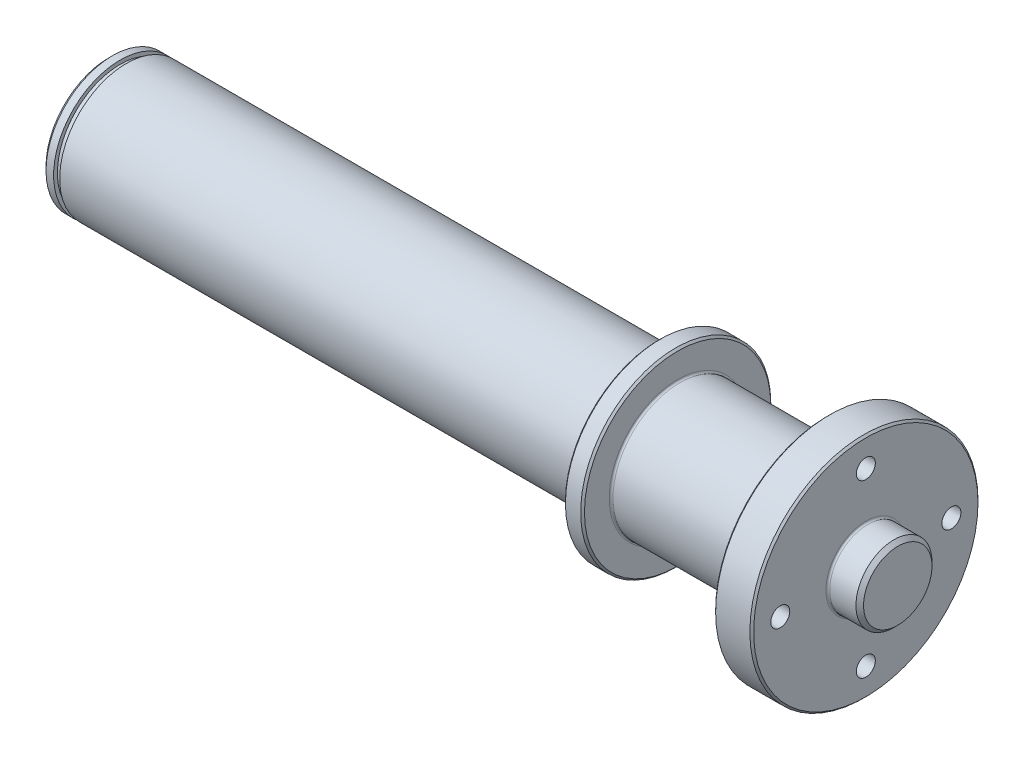
SolidWorks part; units mm, degrees
material "1.0037 (S235JR)"
ref_plane "Płaszczyzna przednia" through (0, 0, 0) normal (0, 0, 1) x (1, 0, 0)
ref_plane "Płaszczyzna górna" through (0, 0, 0) normal (0, 1, 0) x (1, 0, 0)
ref_plane "Płaszczyzna prawa" through (0, 0, 0) normal (1, 0, 0) x (0, 0, -1)
sketch "Szkic1" plane through (0, 0, 0) normal (0, 0, 1) x (1, 0, 0)
  line L0 (0, 0) -> (207.5, 0)
  line L1 (0, 0) -> (0, 17.5)
  line L2 (0, 17.5) -> (3, 17.5)
  line L3 (3, 17.5) -> (3, 16.5)
  line L4 (3, 16.5) -> (4.6, 16.5)
  line L5 (4.6, 16.5) -> (4.6, 17.5)
  line L6 (4.6, 17.5) -> (144.6, 17.5)
  line L7 (144.6, 17.5) -> (144.6, 25)
  line L8 (144.6, 25) -> (149.6, 25)
  line L9 (149.6, 25) -> (149.6, 17.5)
  line L10 (149.6, 17.5) -> (189.1, 17.5)
  line L11 (189.1, 17.5) -> (189.1, 30)
  line L12 (189.1, 30) -> (199.1, 30)
  line L13 (199.1, 30) -> (199.1, 10)
  line L14 (199.1, 10) -> (207.5, 10)
  line L15 (207.5, 10) -> (207.5, 0)
  line L16 (0, 0) -> (-14.1006, 0) construction
  dimension "D1" = 207.5
  dimension "D2" = 35
  dimension "D3" = 33
  dimension "D5" = 50
  dimension "D6" = 35
  dimension "D7" = 60
  dimension "D8" = 20
  dimension "D9" = 3
  dimension "D10" = 1.6
  dimension "D11" = 140
  dimension "D12" = 5
  dimension "D13" = 54.5
  dimension "D14" = 10
revolve "Obrót1" add sketch "Szkic1" angle 360 about L16
hole_wizard "Otwór gwintowany M63" positions "Szkic4" profile "Szkic6" tap size "M6" standard "DIN" end condition up to next
sketch "Szkic4" plane through (199.1, 0, 0) normal (1, 0, 0) x (0, 0, -1)
  line L0 (0, 0) -> (0, 22.5) construction
  circle A0 centre (0, 0) radius 22.5
  point P0 (0, 22.5)
  point P2 (22.5, 0)
  point P4 (0, -22.5)
  point P6 (-22.5, 0)
  dimension "D1" = 45
sketch "Szkic6" plane through (199.1, 22.5, 0) normal (0, 1, 0) x (0, 0, -1)
  line L0 (0, 0) -> (0, 10)
  line L1 (0, 10) -> (2.5, 10)
  line L2 (2.5, 10) -> (2.5, 0)
  line L5 (2.5, 0) -> (0, 0)
  line L11 (0, -6.35) -> (0, 107.95) construction
  dimension "Średnica otworu gwintowanego na wylot" = 5
  dimension "Głębokość otworu gwintowanego na wylot" = 10
cosmetic thread "Gwint otworu1" parameters "D2"=6
cosmetic thread "Gwint otworu2" parameters "D2"=6
cosmetic thread "Gwint otworu3" parameters "D2"=6
cosmetic thread "Gwint otworu4" parameters "D2"=6
chamfer "Sfazowanie1" distance 1 angle 45 2 edges at (0, 0, -17.5) (207.5, 0, -10)
fillet "Zaokrąglenie1" radius 0.5 3 edges at (189.1, 0, -17.5) (144.6, 0, -17.5) (149.6, 0, -17.5)
chamfer "Sfazowanie2" distance 0.5 angle 45 4 edges at (199.1, 0, -30) (189.1, 0, -30) (149.6, 0, -25) (144.6, 0, -25)
fillet "Zaokrąglenie2" radius 0.5 1 edges at (199.1, 0, -10)
ref_plane "Płaszczyzna1" through (0, 0, -17.5) normal (0, 0, -1) x (-1, 0, 0)
sketch "Szkic7" plane through (0, 0, -17.5) normal (0, 0, -1) x (-1, 0, 0)
  line L0 (-12.1, 0) -> (-42.1, 0) construction
  line L1 (-12.1, -5) -> (-42.1, -5)
  line L2 (-12.1, 5) -> (-42.1, 5)
  line L3 (-4.6, -17.5) -> (-4.6, 17.5) construction
  arc A0 (-12.1, -5) -> (-12.1, 5) centre (-12.1, 0) ccw
  arc A1 (-42.1, 5) -> (-42.1, -5) centre (-42.1, 0) ccw
  point P3 (-27.1, 0)
  dimension "D3" = 7.5
  dimension "D1" = 10
  dimension "D2" = 30
extrude "Wytnij-wyciągnięcie1" cut sketch "Szkic7" against normal blind 5
